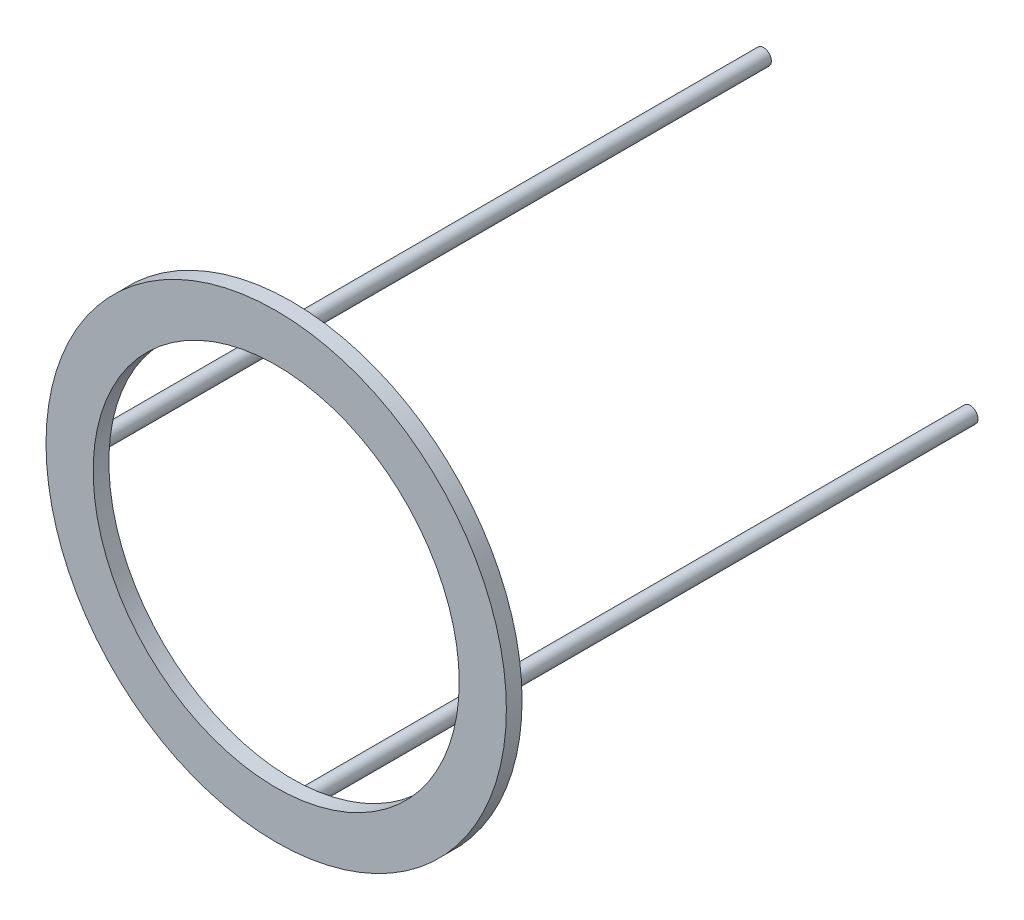
SolidWorks part; units mm, degrees
ref_plane "Front Plane" through (0, 0, 0) normal (0, 0, 1) x (1, 0, 0)
ref_plane "Top Plane" through (0, 0, 0) normal (0, 1, 0) x (1, 0, 0)
ref_plane "Right Plane" through (0, 0, 0) normal (1, 0, 0) x (0, 0, -1)
sketch "Sketch2" plane through (0, 0, 0) normal (0, 0, 1) x (1, 0, 0)
  circle A0 centre (0, 0) radius 146.4214
  circle A1 centre (0, 0) radius 116.4214
  dimension "D1" = 292.8427
  dimension "D2" = 232.8427
extrude "Boss-Extrude1" add sketch "Sketch2" along normal blind 10
sketch "Sketch5" plane through (0, 0, 10) normal (0, 0, 1) x (1, 0, 0)
  line L0 (0, 0) -> (0, 146.4214) construction
  line L1 (0, 0) -> (-146.4214, 0) construction
  line L2 (0, 0) -> (0, -146.4214) construction
  line L3 (0, 0) -> (146.4214, 0) construction
  line L4 (0, 0) -> (-103.5355, 103.5355) construction
  line L5 (0, 0) -> (-103.5355, -103.5355) construction
  line L6 (0, 0) -> (103.5355, -103.5355) construction
  line L7 (0, 0) -> (103.5355, 103.5355) construction
  circle A0 centre (0, 0) radius 131.4214 construction
  circle A1 centre (0, 0) radius 146.4214 construction
  circle A2 centre (-92.9289, 92.9289) radius 4.0979 construction
  circle A3 centre (92.9289, 92.9289) radius 4.6951 construction
  circle A4 centre (92.9289, -92.9289) radius 10.2068 construction
  circle A5 centre (-92.9289, -92.9289) radius 3.8769 construction
  dimension "D1" = 262.8427
sketch "Sketch7" plane through (0, 0, 0) normal (0, 0, -1) x (-1, 0, 0)
  line L1 (0, 0) -> (-146.4214, 0) construction
  line L2 (0, 0) -> (0, 146.4214) construction
  line L3 (0, 0) -> (146.4214, 0) construction
  line L4 (0, 0) -> (0, -146.4214) construction
  circle A2 centre (0, 0) radius 131.4214 construction
  circle A3 centre (-131.4214, 0) radius 5
  circle A4 centre (0, 131.4214) radius 5
  circle A5 centre (131.4214, 0) radius 5
  circle A6 centre (0, -131.4214) radius 5
  point P0 (-131.4214, 0)
  point P5 (0, 131.4214)
  point P6 (131.4214, 0)
  point P9 (0, -131.4214)
extrude "Boss-Extrude3" add sketch "Sketch7" along normal blind 300
equation "\"D1@Sketch2\" = 200* sqr( 2 ) +10"
equation "\"D2@Sketch2\" = \"D1@Sketch2\"-60"
equation "\"D1@Sketch5\" = (\"D1@Sketch2\"+\"D2@Sketch2\")/2"
equation "\"D1@Boss-Extrude3\"=300"
